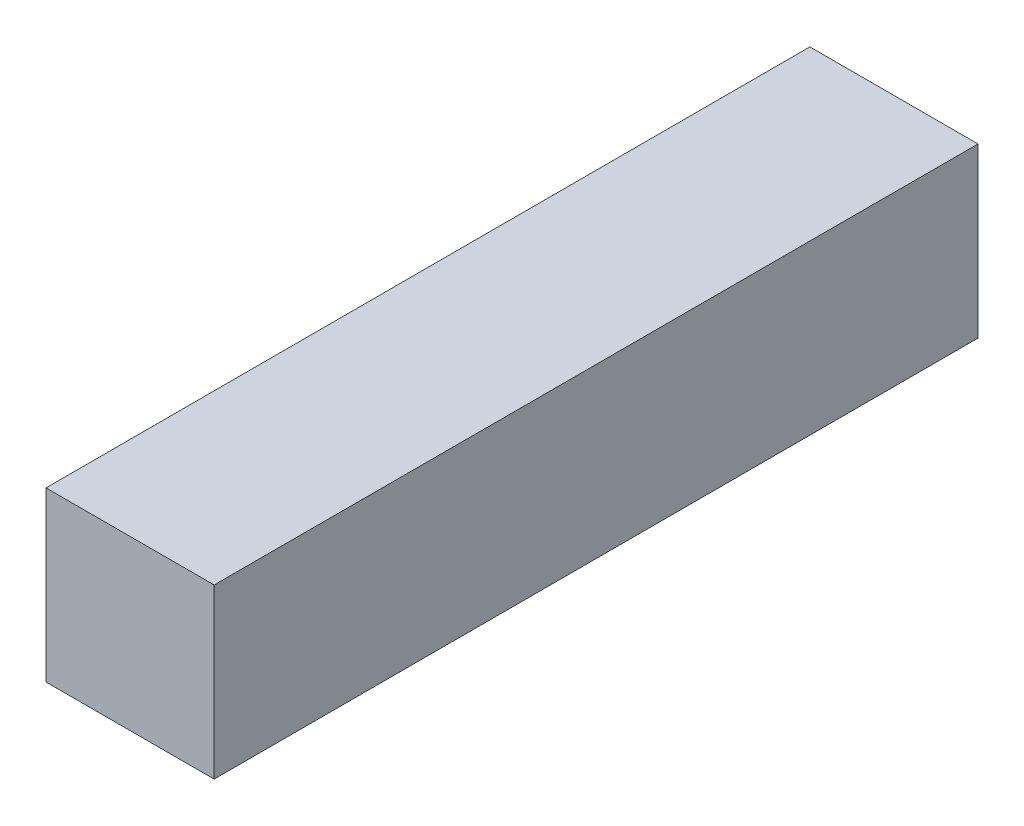
SolidWorks part; units mm, degrees
material "AISI 1020"
ref_plane "Спереди" through (0, 0, 0) normal (0, 0, 1) x (1, 0, 0)
ref_plane "Сверху" through (0, 0, 0) normal (0, 1, 0) x (1, 0, 0)
ref_plane "Справа" through (0, 0, 0) normal (1, 0, 0) x (0, 0, -1)
sketch "Эскиз1" plane through (0, 0, 0) normal (0, 0, 1) x (1, 0, 0)
  line L1 (-7, 7) -> (0, 7)
  line L2 (-7, 7) -> (-7, 0)
  line L3 (-7, 0) -> (0, 0)
  line L4 (0, 7) -> (0, 0)
extrude "Бобышка-Вытянуть1" add sketch "Эскиз1" against normal up to surface (31.8 mm away)
